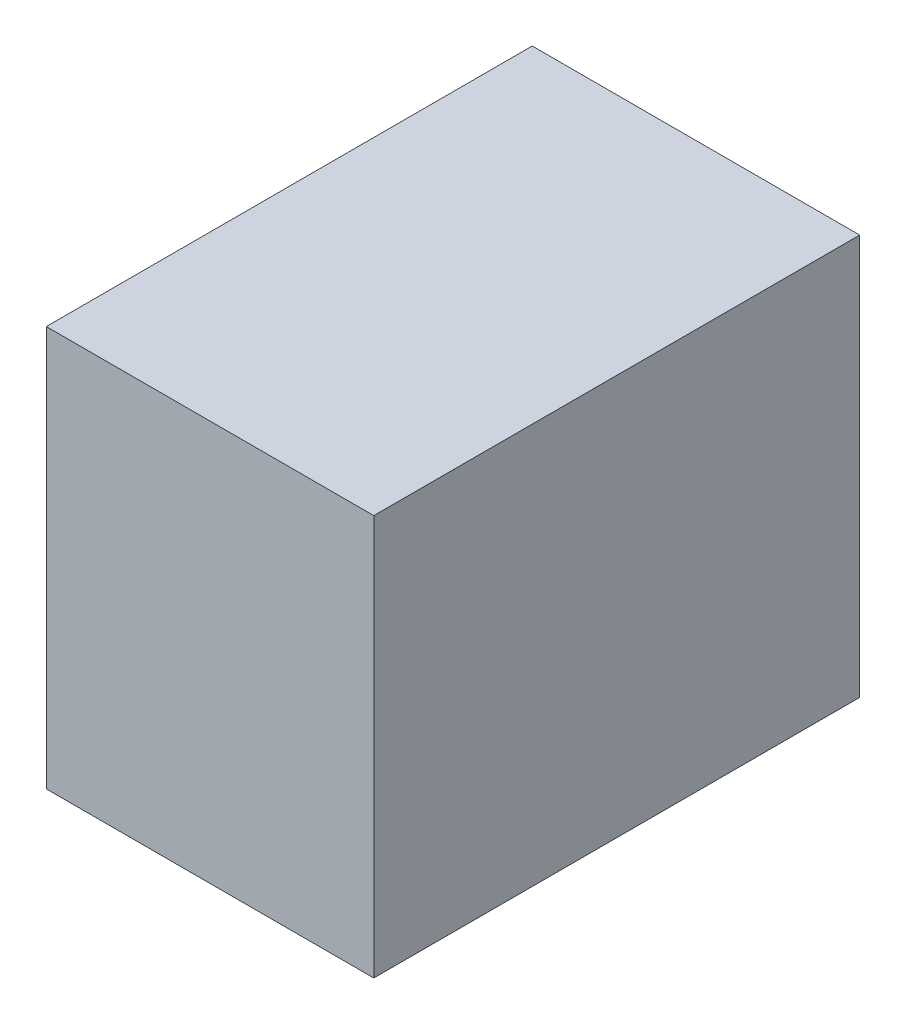
SolidWorks part; units mm, degrees
ref_plane "Front Plane" through (0, 0, 0) normal (0, 0, 1) x (1, 0, 0)
ref_plane "Top Plane" through (0, 0, 0) normal (0, 1, 0) x (1, 0, 0)
ref_plane "Right Plane" through (0, 0, 0) normal (1, 0, 0) x (0, 0, -1)
sketch "Sketch1" plane through (0, 0, 0) normal (0, 1, 0) x (1, 0, 0)
  line L1 (444.5, -659.6062) -> (-444.5, -659.6063)
  line L2 (444.5, -659.6062) -> (444.5, 659.6062)
  line L3 (444.5, 659.6062) -> (-444.5, 659.6062)
  line L4 (-444.5, -659.6063) -> (-444.5, 659.6062)
  line L5 (444.5, -659.6062) -> (-444.5, 659.6062) construction
  line L6 (444.5, 659.6062) -> (-444.5, -659.6063) construction
  point P0 (0, 0)
  dimension "D1" = 889
  dimension "D2" = 1319.2125
extrude "Boss-Extrude1" add sketch "Sketch1" along normal blind 1087.12
